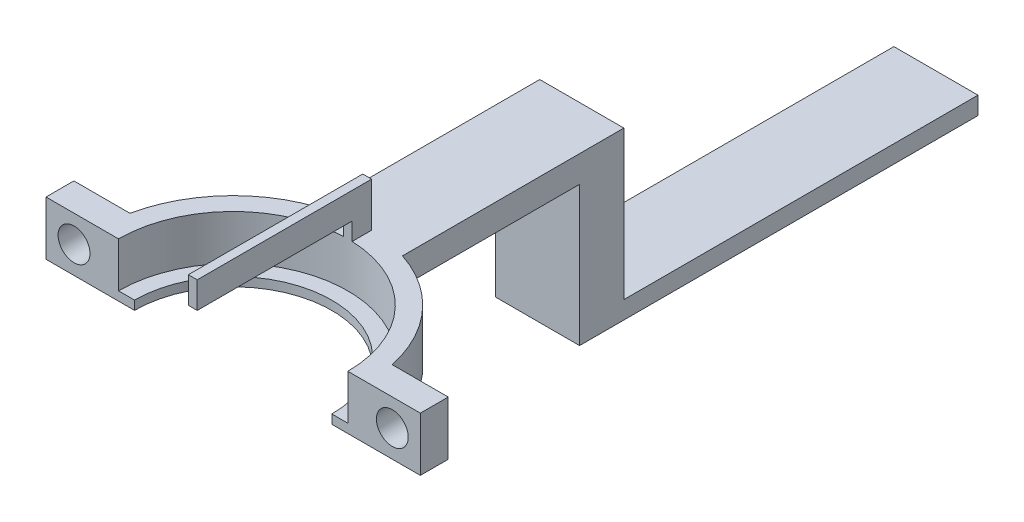
SolidWorks part; units mm, degrees
ref_plane "Front Plane" through (0, 0, 0) normal (0, 0, 1) x (1, 0, 0)
ref_plane "Top Plane" through (0, 0, 0) normal (0, 1, 0) x (1, 0, 0)
ref_plane "Right Plane" through (0, 0, 0) normal (1, 0, 0) x (0, 0, -1)
sketch "Sketch3" plane through (0, 0, 0) normal (0, 0, 1) x (1, 0, 0)
  line L0 (-62.6943, 10.2507) -> (-62.6943, 11.7337)
  line L2 (-62.6943, 11.7337) -> (-64.8845, 11.7337)
  line L5 (-60.8845, 6.6507) -> (-62.6943, 6.6507)
  line L6 (-62.6943, 6.6507) -> (-62.6943, 10.2507)
  line L10 (-64.8845, 11.7337) -> (-64.8845, 5.6398)
  line L11 (-64.8845, 5.6398) -> (-60.8845, 5.6398)
  line L12 (-60.8845, 5.6398) -> (-60.8845, 6.6507)
  dimension "D3" = 4
sketch "Sketch4" plane through (0, 0, 0) normal (0, 0, 1) x (1, 0, 0)
  line L0 (-49.7443, 0) -> (-49.7443, 12.8648) construction
  line L1 (27.6543, 0) -> (-27.6543, 0) construction
revolve "Revolve1" add sketch "Sketch3" angle 360 about L0
sketch "Sketch7" plane through (0, 11.7337, 0) normal (0, 1, 0) x (1, 0, 0)
  line L2 (-50.2443, 15.132) -> (-50.2443, 12.9403)
  line L3 (-49.2443, 15.132) -> (-49.2443, 12.9403)
  circle A0 centre (-49.7443, 0) radius 15.1403 construction
  arc A1 (-49.2443, 15.132) -> (-50.2443, 15.132) centre (-49.7443, 0) ccw
  circle A2 centre (-49.7443, 0) radius 12.95 construction
  arc A3 (-49.2443, 12.9403) -> (-50.2443, 12.9403) centre (-49.7443, 0) ccw
  point P9 (-49.7443, 14.131)
  dimension "D1" = 1
extrude "Boss-Extrude1" add sketch "Sketch7" along normal blind 5
sketch "Sketch8" plane through (0, 16.7337, 0) normal (0, 1, 0) x (1, 0, 0)
  line L0 (-50.2443, 15.132) -> (-50.2443, 12.9403) construction
  line L3 (-50.2443, 15.132) -> (-50.2443, 12.9403)
  line L4 (-49.2443, 12.9403) -> (-49.2443, 15.132) construction
  line L5 (-49.2443, 12.9403) -> (-49.2443, 15.132)
  line L6 (-50.2443, 12.9403) -> (-50.2443, -4.5597)
  line L7 (-50.2443, -4.5597) -> (-49.2443, -4.5597)
  line L8 (-49.2443, -4.5597) -> (-49.2443, 12.9403)
  arc A0 (-49.2443, 15.132) -> (-50.2443, 15.132) centre (-49.7443, 0) ccw construction
  arc A1 (-49.2443, 15.132) -> (-50.2443, 15.132) centre (-49.7443, 0) ccw
  dimension "D1" = 17.5
extrude "Boss-Extrude2" add sketch "Sketch8" against normal blind 3
sketch "Sketch9" plane through (0, 11.7337, 0) normal (0, 1, 0) x (1, 0, 0)
  line L2 (-54.4943, 14.3759) -> (-54.4943, 39.3759)
  line L3 (-54.4943, 39.3759) -> (-44.9943, 39.3759)
  line L4 (-44.9943, 39.3759) -> (-44.9943, 14.3759)
  arc A0 (-50.2443, 15.132) -> (-49.2443, 15.132) centre (-49.7443, 0) ccw construction
  arc A1 (-50.2443, 15.132) -> (-54.4943, 14.3759) centre (-49.7443, 0) ccw
  arc A2 (-49.2443, 15.132) -> (-50.2443, 15.132) centre (-49.7443, 0) ccw construction
  arc A3 (-49.2443, 15.132) -> (-50.2443, 15.132) centre (-49.7443, 0) ccw
  arc A4 (-44.9943, 14.3759) -> (-49.2443, 15.132) centre (-49.7443, 0) ccw
  point P9 (-49.7443, 0)
  dimension "D1" = 25
extrude "Boss-Extrude3" add sketch "Sketch9" against normal blind 3
sketch "Sketch10" plane through (0, 8.7337, 0) normal (0, -1, 0) x (1, 0, 0)
  line L0 (-44.9943, -14.3759) -> (-44.9943, -39.3759) construction
  line L1 (-54.4943, -39.3759) -> (-44.9943, -39.3759)
  line L2 (-54.4943, -39.3759) -> (-54.4943, -34.3759)
  line L3 (-54.4943, -34.3759) -> (-44.9943, -34.3759)
  line L4 (-44.9943, -39.3759) -> (-44.9943, -34.3759)
  dimension "D1" = 5
extrude "Boss-Extrude4" add sketch "Sketch10" along normal blind 15.78
sketch "Sketch11" plane through (0, 0, -39.3759) normal (0, 0, -1) x (-1, 0, 0)
  line L0 (54.4943, -7.0463) -> (54.4943, 11.7337) construction
  line L1 (44.9943, -7.0463) -> (54.4943, -7.0463)
  line L2 (44.9943, -7.0463) -> (44.9943, -5.0463)
  line L3 (44.9943, -5.0463) -> (54.4943, -5.0463)
  line L4 (54.4943, -7.0463) -> (54.4943, -5.0463)
  dimension "D1" = 2
extrude "Boss-Extrude5" add sketch "Sketch11" along normal blind 40
sketch "Sketch13" plane through (0, 11.7337, 0) normal (0, 1, 0) x (1, 0, 0)
  line L2 (-49.7443, 3.15) -> (-49.7443, -3.15) construction
  line L3 (-28.604, 3.15) -> (-34.9353, 3.15)
  line L4 (-70.8845, 3.15) -> (-70.8845, -3.15)
  line L5 (-70.8845, -3.15) -> (-64.5532, -3.15)
  line L6 (-28.604, -3.15) -> (-28.604, 3.15)
  line L7 (-64.5532, 3.15) -> (-70.8845, 3.15)
  line L8 (-34.9353, -3.15) -> (-28.604, -3.15)
  arc A0 (-54.4943, 14.3759) -> (-44.9943, 14.3759) centre (-49.7443, 0) ccw construction
  arc A1 (-64.5532, 3.15) -> (-64.5532, -3.15) centre (-49.7443, 0) ccw
  arc A2 (-34.9353, -3.15) -> (-34.9353, 3.15) centre (-49.7443, 0) ccw
  point P10 (-49.7443, 0)
  point P13 (-49.7443, 3.15)
  dimension "D1" = 6.3
extrude "Boss-Extrude6" add sketch "Sketch13" against normal up to surface (6.0939 mm away) up to face at (-49.7443, 5.6398, -11.1403)
sketch "Sketch14" plane through (0, 0, 3.15) normal (0, 0, 1) x (1, 0, 0)
  line L0 (-70.8845, 11.7337) -> (-64.5532, 5.6398) construction
  line L1 (-28.604, 11.7337) -> (-34.9353, 5.6398) construction
  circle A0 centre (-31.7697, 8.6868) radius 1.8
  circle A1 centre (-67.7189, 8.6868) radius 1.8
  dimension "D1" = 3.6
  dimension "D2" = 3.6
extrude "Cut-Extrude1" cut sketch "Sketch14" against normal up to surface (6.3 mm away) contours A1 | A0 up to face at (-67.7189, 8.6868, -3.15)
sketch "Sketch15" plane through (0, 11.7337, 0) normal (0, 1, 0) x (1, 0, 0)
  line L0 (-70.8845, 0) -> (-23.4421, 0) construction
  line L1 (-70.8845, 3.15) -> (-70.8845, -3.15) construction
  line L2 (-9.2036, 0) -> (9.2036, 0) construction
  line L4 (-23.4421, 0) -> (-74.5953, 0)
  line L5 (-23.4421, 0) -> (-23.4421, -31.9022)
  line L6 (-23.4421, -31.9022) -> (-74.5953, -31.9022)
  line L7 (-74.5953, 0) -> (-74.5953, -31.9022)
extrude "Cut-Extrude3" cut sketch "Sketch15" against normal through all
